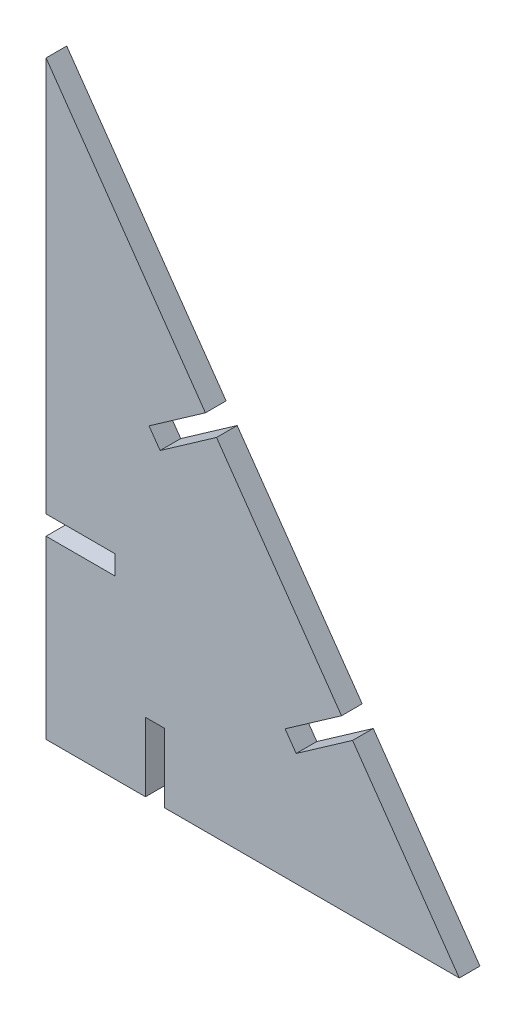
SolidWorks part; units mm, degrees
ref_plane "Plan de face" through (0, 0, 0) normal (0, 0, 1) x (1, 0, 0)
ref_plane "Plan de dessus" through (0, 0, 0) normal (0, 1, 0) x (1, 0, 0)
ref_plane "Plan de droite" through (0, 0, 0) normal (1, 0, 0) x (0, 0, -1)
sketch "Esquisse1" plane through (0, 0, 0) normal (0, 0, 1) x (1, 0, 0)
  line L0 (0, 0) -> (14.4345, 0)
  line L1 (60, 0) -> (44.5057, 22.1281)
  line L2 (0, 85.6889) -> (0, 28.3534)
  line L3 (17.2345, 0) -> (60, 0)
  line L5 (14.4345, 0) -> (14.4345, 10)
  line L6 (14.4345, 10) -> (17.2345, 10)
  line L7 (17.2345, 0) -> (17.2345, 10)
  line L9 (0, 25.5534) -> (10, 25.5534)
  line L11 (0, 28.3534) -> (10, 28.3534)
  line L12 (10, 25.5534) -> (10, 28.3534)
  line L13 (44.5057, 22.1281) -> (36.3142, 16.3924)
  line L14 (42.8997, 24.4218) -> (34.7082, 18.686)
  line L15 (36.3142, 16.3924) -> (34.7082, 18.686)
  line L17 (24.7496, 50.3428) -> (16.5581, 44.6071)
  line L18 (23.1436, 52.6364) -> (14.952, 46.9007)
  line L19 (16.5581, 44.6071) -> (14.952, 46.9007)
  line L20 (23.1436, 52.6364) -> (0, 85.6889)
  line L21 (42.8997, 24.4218) -> (24.7496, 50.3428)
  line L22 (0, 25.5534) -> (0, 0)
  dimension "D1" = 60
  dimension "D2" = 55
  dimension "D3" = 10
  dimension "D4" = 2.8
  dimension "D5" = 10
  dimension "D6" = 2.8
  dimension "D7" = 2.8
  dimension "D8" = 10
  dimension "D9" = 10
  dimension "D10" = 2.8
extrude "Boss.-Extru.1" add sketch "Esquisse1" along normal blind 3
